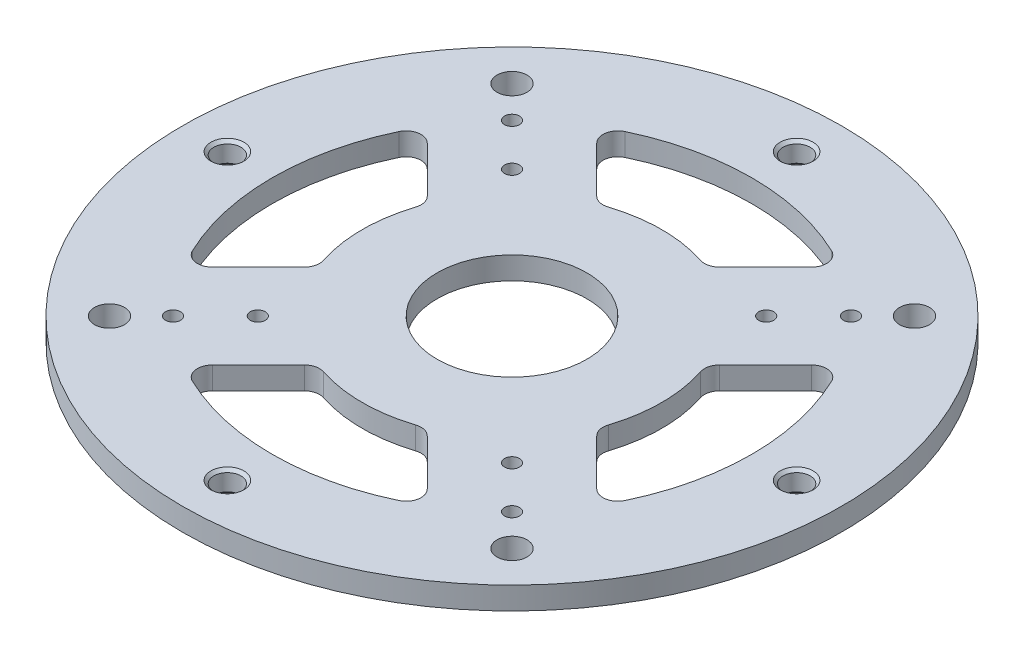
SolidWorks part; units mm, degrees
material "6061-T4 (SS)"
ref_plane "Front Plane" through (0, 0, 0) normal (0, 0, 1) x (1, 0, 0)
ref_plane "Top Plane" through (0, 0, 0) normal (0, 1, 0) x (1, 0, 0)
ref_plane "Right Plane" through (0, 0, 0) normal (1, 0, 0) x (0, 0, -1)
sketch "Sketch2" plane through (0, 0, 0) normal (0, 1, 0) x (1, 0, 0)
  line L0 (0, 0) -> (0, 114.3) construction
  line L3 (22.4506, 22.4506) -> (98.7828, 98.7828) construction
  line L4 (61.9546, 26.0336) -> (81.4605, 45.5395)
  line L5 (26.0336, 61.9546) -> (45.5395, 81.4605)
  line L7 (61.9546, -26.0336) -> (81.4605, -45.5395)
  line L8 (4.4901, 40.4112) -> (80.8223, 116.7433) construction
  line L9 (40.4112, 4.4901) -> (116.7433, 80.8223) construction
  line L10 (26.0336, -61.9546) -> (45.5395, -81.4605)
  line L11 (-26.0336, -61.9546) -> (-45.5395, -81.4605)
  line L12 (-61.9546, -26.0336) -> (-81.4605, -45.5395)
  line L13 (-61.9546, 26.0336) -> (-81.4605, 45.5395)
  line L14 (-26.0336, 61.9546) -> (-45.5395, 81.4605)
  arc A0 (-91.6807, 43.786) -> (-91.6807, -43.786) centre (0, 0) ccw
  circle A1 centre (0, 0) radius 139.7
  arc A2 (43.786, 91.6807) -> (-43.786, 91.6807) centre (0, 0) ccw
  arc A3 (91.6807, -43.786) -> (91.6807, 43.786) centre (0, 0) ccw
  arc A4 (-43.786, -91.6807) -> (43.786, -91.6807) centre (0, 0) ccw
  arc A5 (-19.585, -60.4043) -> (19.585, -60.4043) centre (0, 0) ccw
  arc A6 (-81.4605, 45.5395) -> (-91.6807, 43.786) centre (-85.9506, 41.0494) ccw
  arc A7 (-91.6807, -43.786) -> (-81.4605, -45.5395) centre (-85.9506, -41.0494) ccw
  arc A8 (-45.5395, -81.4605) -> (-43.786, -91.6807) centre (-41.0494, -85.9506) ccw
  arc A9 (43.786, -91.6807) -> (45.5395, -81.4605) centre (41.0494, -85.9506) ccw
  arc A10 (60.4043, -19.585) -> (60.4043, 19.585) centre (0, 0) ccw
  arc A11 (19.585, 60.4043) -> (-19.585, 60.4043) centre (0, 0) ccw
  arc A12 (81.4605, -45.5395) -> (91.6807, -43.786) centre (85.9506, -41.0494) ccw
  arc A13 (91.6807, 43.786) -> (81.4605, 45.5395) centre (85.9506, 41.0494) ccw
  arc A14 (-60.4043, -19.585) -> (-61.9546, -26.0336) centre (-66.4447, -21.5435) cw
  arc A15 (45.5395, 81.4605) -> (43.786, 91.6807) centre (41.0494, 85.9506) ccw
  arc A16 (-43.786, 91.6807) -> (-45.5395, 81.4605) centre (-41.0494, 85.9506) ccw
  arc A17 (-60.4043, 19.585) -> (-60.4043, -19.585) centre (0, 0) ccw
  circle A18 centre (0, 0) radius 31.75
  arc A19 (-26.0336, -61.9546) -> (-19.585, -60.4043) centre (-21.5435, -66.4447) cw
  arc A20 (19.585, -60.4043) -> (26.0336, -61.9546) centre (21.5435, -66.4447) cw
  arc A21 (61.9546, -26.0336) -> (60.4043, -19.585) centre (66.4447, -21.5435) cw
  arc A22 (60.4043, 19.585) -> (61.9546, 26.0336) centre (66.4447, 21.5435) cw
  arc A23 (26.0336, 61.9546) -> (19.585, 60.4043) centre (21.5435, 66.4447) cw
  arc A24 (-19.585, 60.4043) -> (-26.0336, 61.9546) centre (-21.5435, 66.4447) cw
  arc A25 (-61.9546, 26.0336) -> (-60.4043, 19.585) centre (-66.4447, 21.5435) cw
  point P28 (-51.6003, -87.5213)
  point P29 (0, 0)
  point P39 (87.5213, -51.6003)
  point P43 (-23.1922, -59.1132)
  point P47 (51.6003, 87.5213)
  point P52 (23.1922, -59.1132)
  point P55 (59.1132, -23.1922)
  point P58 (59.1132, 23.1922)
  point P61 (23.1922, 59.1132)
  dimension "D2" = 279.4
  dimension "D5" = 127
  dimension "D4" = 203.2
  dimension "D9" = 63.5
  dimension "D10" = 6.35
  dimension "D13" = 6.35
  dimension "D3" = 45
  dimension "D8" = 50.8
  dimension "D11" = 66.4447
  dimension "D12" = 66.4447
  dimension "D6" = 25.4
  dimension "D7" = 4
extrude "Boss-Extrude1" add sketch "Sketch2" along normal blind 9.525
sketch "Sketch3" plane through (0, 9.525, 0) normal (0, 1, 0) x (1, 0, 0)
  line L0 (0, 0) -> (0, 120.65) construction
  line L1 (0, 0) -> (85.3124, 85.3124) construction
  line L2 (85.3124, 85.3124) -> (103.2729, 103.2729) construction
  line L3 (0, 0) -> (-53.8815, 53.8815) construction
  line L4 (-53.8815, 53.8815) -> (-71.842, 71.842) construction
  circle A0 centre (-71.842, 71.842) radius 3.175
  circle A1 centre (0, 0) radius 120.65 construction
  circle A2 centre (0, 120.65) radius 7.1437
  circle A3 centre (120.65, 0) radius 7.1438
  circle A4 centre (0, -120.65) radius 7.1437
  circle A5 centre (-120.65, 0) radius 7.1438
  circle A6 centre (0, 0) radius 120.65 construction
  circle A10 centre (0, 0) radius 139.7 construction
  circle A17 centre (-53.8815, 53.8815) radius 3.175
  circle A18 centre (-71.842, -71.842) radius 3.175
  circle A19 centre (71.842, -71.842) radius 3.175
  circle A20 centre (71.842, 71.842) radius 3.175
  circle A21 centre (53.8815, 53.8815) radius 3.175
  circle A22 centre (53.8815, -53.8815) radius 3.175
  circle A23 centre (-53.8815, -53.8815) radius 3.175
  circle A24 centre (85.3124, 85.3124) radius 6.35
  circle A25 centre (85.3124, -85.3124) radius 6.35
  circle A26 centre (-85.3124, -85.3124) radius 6.35
  circle A27 centre (-85.3124, 85.3124) radius 6.35
  point P17 (0, 0)
  point P26 (0, 0)
  point P39 (0, 0)
  point P47 (0, 0)
  point P54 (0, 0)
  point P63 (0, 0)
  dimension "D2" = 14.2875
  dimension "D5" = 120.65
  dimension "D6" = 76.2
  dimension "D7" = 241.3
  dimension "D9" = 25.4
  dimension "D13" = 12.7
  dimension "D14" = 45
  dimension "D15" = 4
  dimension "D4" = 45
  dimension "D3" = 4
  dimension "D11" = 4
  dimension "D12" = 4
extrude "Cut-Extrude2" cut sketch "Sketch3" against normal through all
sketch "Sketch4" plane through (0, 9.525, 0) normal (0, 1, 0) x (1, 0, 0)
  line L1 (-152.4, -152.4) -> (152.4, -152.4) construction
  line L2 (-152.4, -152.4) -> (-152.4, 152.4) construction
  line L3 (-152.4, 152.4) -> (152.4, 152.4) construction
  line L4 (152.4, -152.4) -> (152.4, 152.4) construction
  line L5 (-152.4, -152.4) -> (152.4, 152.4) construction
  line L6 (-152.4, 152.4) -> (152.4, -152.4) construction
  point P0 (0, 0)
  dimension "D1" = 304.8
sketch "Sketch5" plane through (0, 9.525, 0) normal (0, 1, 0) x (1, 0, 0)
  circle A1 centre (0, 0) radius 139.7
  circle A2 centre (0, 0) radius 139.7
  circle A3 centre (0, -120.65) radius 7.1437
  circle A4 centre (0, -120.65) radius 7.1437
  circle A5 centre (120.65, 0) radius 7.1438
  circle A6 centre (120.65, 0) radius 7.1438
  circle A7 centre (0, 120.65) radius 7.1437
  circle A8 centre (0, 120.65) radius 7.1437
  circle A9 centre (-71.842, 71.842) radius 3.175
  circle A10 centre (-71.842, 71.842) radius 3.175
  circle A11 centre (85.3124, 85.3124) radius 6.35
  circle A12 centre (85.3124, 85.3124) radius 6.35
  circle A13 centre (-53.8815, 53.8815) radius 3.175
  circle A14 centre (-53.8815, 53.8815) radius 3.175
  circle A15 centre (-120.65, 0) radius 7.1438
  circle A16 centre (-120.65, 0) radius 7.1438
  circle A17 centre (71.842, 71.842) radius 3.175
  circle A18 centre (71.842, 71.842) radius 3.175
  circle A19 centre (71.842, -71.842) radius 3.175
  circle A20 centre (71.842, -71.842) radius 3.175
  circle A21 centre (-71.842, -71.842) radius 3.175
  circle A22 centre (-71.842, -71.842) radius 3.175
  circle A23 centre (-85.3124, 85.3124) radius 6.35
  circle A24 centre (-85.3124, 85.3124) radius 6.35
  circle A25 centre (-85.3124, -85.3124) radius 6.35
  circle A26 centre (-85.3124, -85.3124) radius 6.35
  circle A27 centre (85.3124, -85.3124) radius 6.35
  circle A28 centre (85.3124, -85.3124) radius 6.35
  circle A29 centre (-53.8815, -53.8815) radius 3.175
  circle A30 centre (-53.8815, -53.8815) radius 3.175
  circle A31 centre (53.8815, -53.8815) radius 3.175
  circle A32 centre (53.8815, -53.8815) radius 3.175
  circle A33 centre (53.8815, 53.8815) radius 3.175
  circle A34 centre (53.8815, 53.8815) radius 3.175
  dimension "D1" = 0
  dimension "D2" = 0
  dimension "D3" = 0
  dimension "D4" = 0
  dimension "D5" = 0
  dimension "D6" = 0
  dimension "D7" = 0
  dimension "D8" = 0
  dimension "D9" = 0
  dimension "D10" = 0
  dimension "D11" = 0
  dimension "D12" = 0
  dimension "D13" = 0
  dimension "D14" = 0
  dimension "D15" = 0
  dimension "D16" = 0
  dimension "D17" = 0
hole_wizard "1/2-20 Tapped Hole1" positions "Sketch6" profile "Sketch7" tap size "1/2-20" standard "ANSI Inch" end condition through all
sketch "Sketch6" plane through (0, 9.525, 0) normal (0, 1, 0) x (1, 0, 0)
  point P0 (-120.65, 0)
  point P3 (0, 120.65)
  point P6 (120.65, 0)
  point P9 (0, -120.65)
sketch "Sketch7" plane through (-120.65, 9.525, 0) normal (1, 0, 0) x (0, 0, 1)
  line L0 (0, 0) -> (0, 9.525)
  line L1 (0, 9.525) -> (6.985, 9.525)
  line L2 (5.7544, 8.2944) -> (5.7544, 1.2306)
  line L3 (5.7544, 1.2306) -> (6.985, 0)
  line L5 (6.985, 0) -> (0, 0)
  line L6 (-5.7544, 1.2306) -> (-6.985, 0) construction
  line L7 (6.985, 9.525) -> (5.7544, 8.2944)
  line L8 (-6.985, 9.525) -> (-5.7544, 8.2944) construction
  line L11 (0, -6.35) -> (0, 107.95) construction
  dimension "Thru Tap Drill Dia." = 11.5087
  dimension "Thru Tap Drill Depth" = 9.525
  dimension "Near C'Sink Dia." = 13.97
  dimension "Near C'Sink Angle" = 90
  dimension "Far C'Sink Dia." = 13.97
  dimension "Far C'Sink Angle" = 90
cosmetic thread "Hole Thread1" parameters "D2"=12.7
cosmetic thread "Hole Thread2" parameters "D2"=12.7
cosmetic thread "Hole Thread3" parameters "D2"=12.7
cosmetic thread "Hole Thread4" parameters "D2"=12.7
